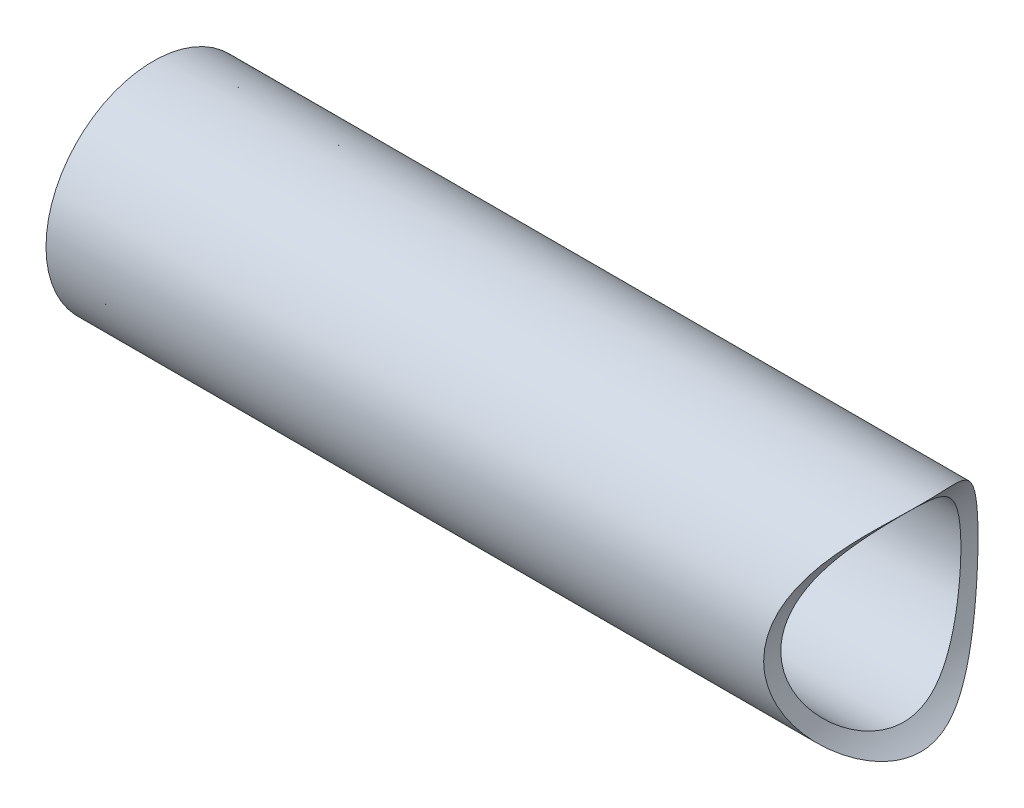
SolidWorks part; units mm, degrees
ref_plane "Front Plane" through (0, 0, 0) normal (0, 0, 1) x (1, 0, 0)
ref_plane "Top Plane" through (0, 0, 0) normal (0, 1, 0) x (1, 0, 0)
ref_plane "Right Plane" through (0, 0, 0) normal (1, 0, 0) x (0, 0, -1)
sketch "Sketch1" plane through (0, 0, 0) normal (1, 0, 0) x (0, 0, -1)
  circle A0 centre (0, 0) radius 9.525
  dimension "D1" = 19.05
extrude "Boss-Extrude1" add sketch "Sketch1" along normal blind 76.2
sketch "Sketch3" plane through (0, 0, 0) normal (-1, 0, 0) x (0, 0, 1)
  circle A0 centre (0, 0) radius 8.509
  dimension "D1" = 17.018
extrude "Cut-Extrude1" cut sketch "Sketch3" against normal blind 1.524
sketch "Sketch4" plane through (1.524, 0, 0) normal (-1, 0, 0) x (0, 0, 1)
  circle A0 centre (0, 0) radius 8.001
  dimension "D1" = 16.002
extrude "Cut-Extrude2" cut sketch "Sketch4" against normal through all
ref_plane "Plane1" through (0, 0, 9.525) normal (0, 0, 1) x (1, 0, 0)
sketch "Sketch5" plane through (0, 0, 9.525) normal (0, 0, 1) x (1, 0, 0)
  line L0 (0, 0) -> (86.3206, 0) construction
  line L1 (76.2, -9.525) -> (76.2, 19.6957) construction
  circle A0 centre (76.2, 0) radius 12.4206
  dimension "D1" = 24.8412
extrude "Cut-Extrude3" cut sketch "Sketch5" against normal blind 254
